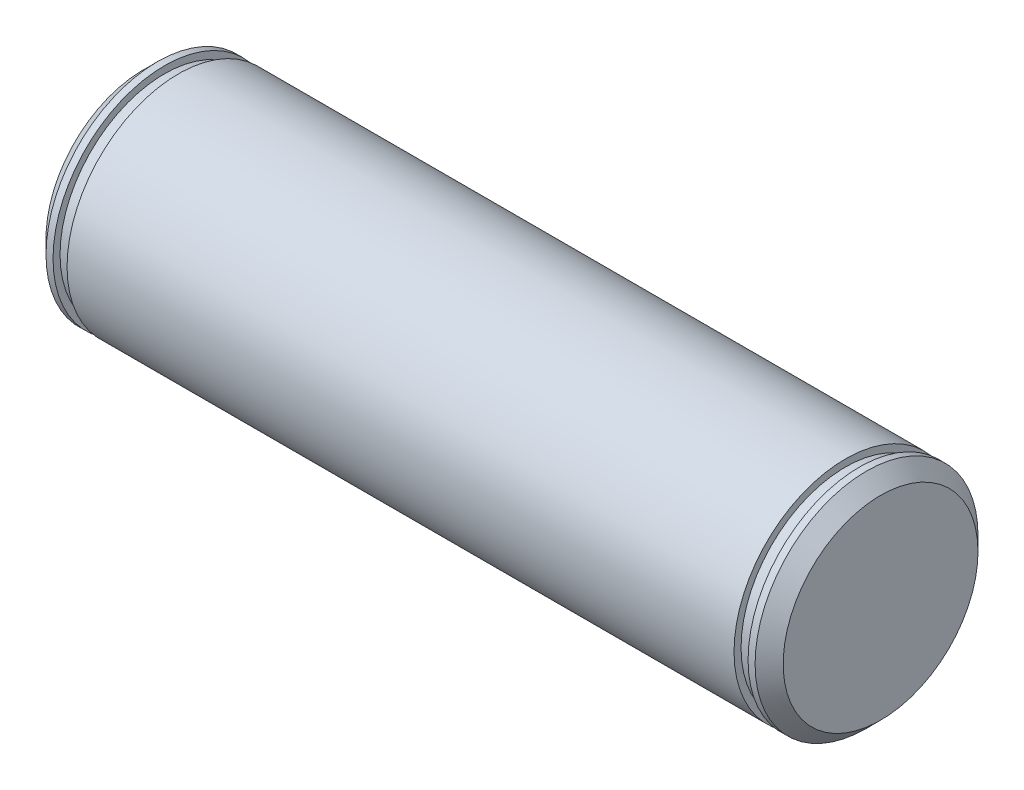
SolidWorks part; units mm, degrees
ref_plane "Front Plane" through (0, 0, 0) normal (0, 0, 1) x (1, 0, 0)
ref_plane "Top Plane" through (0, 0, 0) normal (0, 1, 0) x (1, 0, 0)
ref_plane "Right Plane" through (0, 0, 0) normal (1, 0, 0) x (0, 0, -1)
sketch "Sketch1" plane through (0, 0, 0) normal (1, 0, 0) x (0, 0, -1)
  circle A0 centre (0, 0) radius 15.875
  dimension "D1" = 31.75
extrude "Boss-Extrude1" add sketch "Sketch1" along normal mid plane 105
chamfer "Chamfer1" distance 2 angle 45 2 edges at (-52.5, 0, -15.875) (52.5, 0, -15.875)
ref_plane "Plane1" through (-47.5, 0, 0) normal (-1, 0, 0) x (0, 0, 1)
sketch "Sketch2" plane through (-47.5, 0, 0) normal (-1, 0, 0) x (0, 0, 1)
  circle A0 centre (0, 0) radius 15.875
  circle A1 centre (0, 0) radius 14.875
  dimension "D1" = 31.75
  dimension "D2" = 29.75
extrude "Cut-Extrude1" cut sketch "Sketch2" along normal blind 2
mirror "Mirror1" about plane through (0, 0, 0) normal (1, 0, 0) of "Cut-Extrude1"
